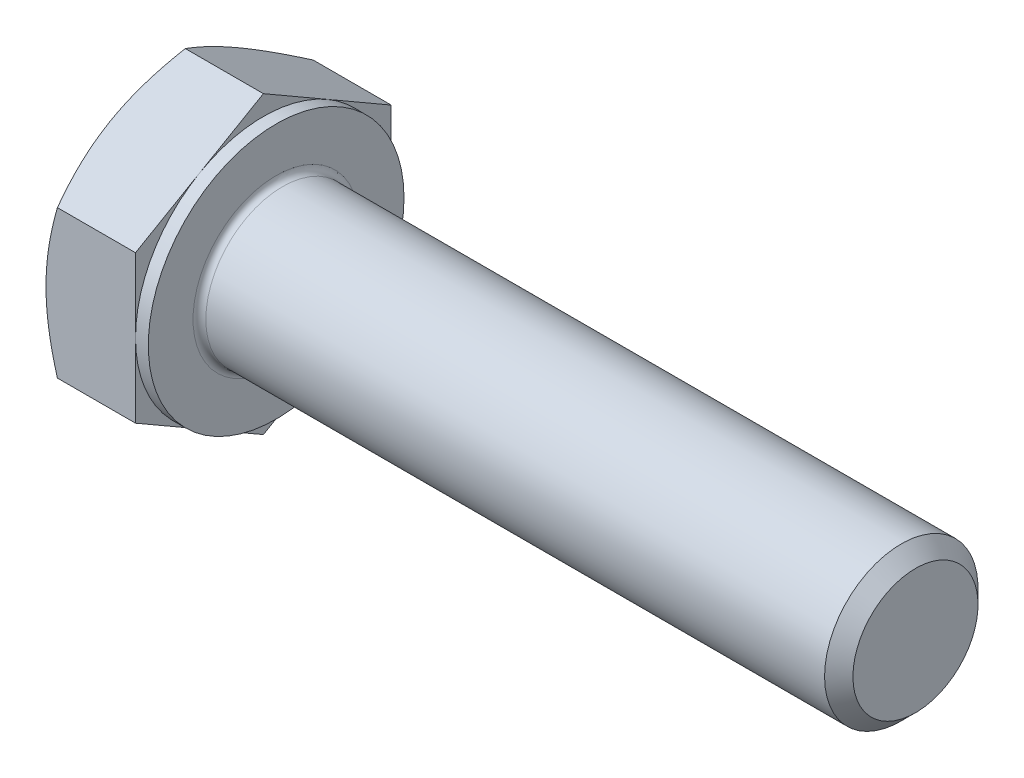
SolidWorks part; units mm, degrees
ref_plane "Plane1" through (0, 0, 0) normal (0, 0, 1) x (1, 0, 0)
ref_plane "Plane2" through (0, 0, 0) normal (0, 1, 0) x (1, 0, 0)
ref_plane "Plane3" through (0, 0, 0) normal (1, 0, 0) x (0, 0, -1)
sketch "Sketch1" plane through (0, 0, 0) normal (1, 0, 0) x (0, 0, -1)
  line L0 (5, 2.8868) -> (5, -2.8868)
  line L1 (-5, 2.8868) -> (-5, -2.8868)
  line L2 (5, -2.8868) -> (0, -5.7735)
  line L3 (0, -5.7735) -> (-5, -2.8868)
  line L4 (5, 2.8868) -> (0, 5.7735)
  line L5 (0, 5.7735) -> (-5, 2.8868)
  dimension "Width_flats" = 10
  dimension "D2" = 120
  dimension "D3" = 5
  dimension "D4" = 5
  dimension "D5" = 5
extrude "BaseHead" add sketch "Sketch1" along normal blind 4
sketch "BodySke" plane through (0, 0, 0) normal (0, 0, 1) x (1, 0, 0)
  line L0 (0, 2.8868) -> (0, -2.8868) construction
  line L1 (0, 0) -> (29, 0)
  line L2 (0, 0) -> (0, 3)
  line L3 (0, 3) -> (28.4455, 3)
  line L4 (29, 0) -> (29, 2.4455)
  line L5 (4, 5.7735) -> (4, 2.8868) construction
  line L6 (29, 2.4455) -> (28.4455, 3)
  line L7 (0, 0) -> (96.52, 0) construction
  line L8 (29, -2.4455) -> (28.4455, -3) construction
  line L9 (0, -3) -> (28.4455, -3) construction
  line L10 (5, 15.24) -> (5, -1.27) construction
  line L12 (4, 2.8868) -> (4, -2.8868) construction
  dimension "Length" = 25
  dimension "Body_ch_ang" = 45
  dimension "Diameter" = 6
  dimension "Minor_dia" = 4.891
  dimension "Advance" = 1
revolve "BaseBody" add sketch "BodySke"
cosmetic thread "ThreadCosmetic" [suppressed]
fillet "HeadFillet" radius 0.25 1 edges at (4, 0, -3)
sketch "Sketch3" plane through (0, 0, 0) normal (0, 0, 1) x (1, 0, 0)
  line L0 (0, 5) -> (3.3333, 10.7735)
  line L1 (0, 5.7735) -> (0, 2.8868) construction
  line L2 (3.3333, 10.7735) -> (3.3333, 15.7735)
  line L3 (3.3333, 15.7735) -> (-10, 15.7735)
  line L4 (-10, 15.7735) -> (-10, 5)
  line L5 (-10, 5) -> (0, 5)
  line L6 (0, 0) -> (99.06, 0) construction
  line L7 (4, 5.7735) -> (0, 5.7735) construction
  dimension "D1" = 5
  dimension "D2" = 5
  dimension "D3" = 10
  dimension "D4" = 5
  dimension "Head_ch_ang" = 30
revolve "HeadChamfer" cut sketch "Sketch3" angle 360 about L6
sketch "Sketch4" plane through (0, 0, 0) normal (0, 0, 1) x (1, 0, 0)
  line L1 (4, 5.7735) -> (4, 2.8868) construction
  line L2 (4, 5) -> (3.5, 5)
  line L3 (4, 5) -> (4, 15.7735)
  line L4 (4, 15.7735) -> (3.5, 15.7735)
  line L5 (0, 0) -> (95.25, 0) construction
  line L6 (0, 0) -> (96.52, 0) construction
  line L7 (3.5, 5) -> (3.5, 15.7735)
  line L8 (4, 5.7735) -> (0.4466, 5.7735) construction
  dimension "D1" = 10
  dimension "D2" = 10
  dimension "Bearing_ht" = 0.5
revolve "BearingFace" cut sketch "Sketch4" angle 360 about L5
sketch "ThdSchSke" plane through (0, 0, 0) normal (0, 0, 1) x (1, 0, 0)
  line L0 (5, -2.4455) -> (4.6117, -3)
  line L1 (5, -2.4455) -> (5.3883, -3)
  line L2 (5.3883, -3) -> (5.3883, -3.75)
  line L3 (-3.175, 0) -> (5.1513, 0) construction
  line L5 (5.3883, -3.75) -> (4.6117, -3.75)
  line L6 (4.6117, -3.75) -> (4.6117, -3)
  dimension "Thread_minor" = 4.891
  dimension "Diameter" = 6
  dimension "Start" = 5
  dimension "SideAngle" = 55
  dimension "VeeAngle" = 70
  dimension "Overcut" = 7.5
revolve "ThreadSchematic" [suppressed] cut sketch "ThdSchSke" angle 360 about L3
pattern_linear "ThdSchPat" [suppressed]
equation "\"D3@Sketch1\" = \"Width_flats@Sketch1\" / 2"
equation "\"D4@Sketch1\" = \"D3@Sketch1\""
equation "\"D5@Sketch1\" = \"D4@Sketch1\""
equation "\"Thread_minor@ThreadCosmetic\" = \"Minor_dia@BodySke\""
equation "\"D1@Sketch3\" = \"Width_flats@Sketch1\" / 2"
equation "\"D1@Sketch4\" = \"Width_flats@Sketch1\""
equation "\"Thread_length@ThreadCosmetic\" = \"Length@BodySke\" - \"Advance@BodySke\""
equation "\"Thread_minor@ThdSchSke\" = \"Minor_dia@BodySke\""
equation "\"Diameter@ThdSchSke\" = \"Diameter@BodySke\""
equation "\"Overcut@ThdSchSke\" = \"Diameter@BodySke\" * 1.25"
equation "\"Start@ThdSchSke\" = \"Head_ht@BaseHead\" + \"Length@BodySke\" - \"Thread_length@ThreadCosmetic\"  '---Non-countersunk---"
equation "\"Num_threads@ThdSchPat\" = int( \"Thread_length@ThreadCosmetic\" / \"Advance@BodySke\" + 0.999 )  + 1"
equation "\"Advance@ThdSchPat\" = \"Thread_length@ThreadCosmetic\" /  (\"Num_threads@ThdSchPat\" - 1) 'relax it"
equation "\"Num_threads@ThdSchPat\" = \"Num_threads@ThdSchPat\" - sgn( \"Num_threads@ThdSchPat\" - 1) '---chamfered tips only---"
